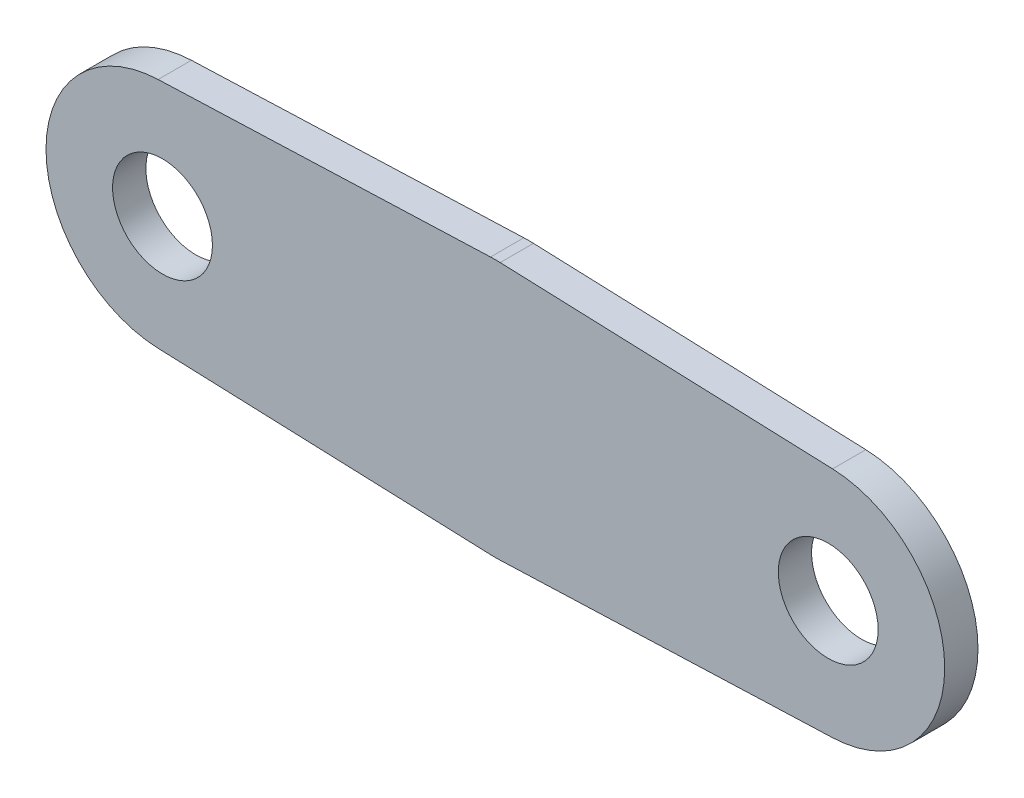
SolidWorks part; units mm, degrees
ref_plane "Płaszczyzna XY" through (0, 0, 0) normal (0, 0, 1) x (1, 0, 0)
ref_plane "Płaszczyzna XZ" through (0, 0, 0) normal (0, 1, 0) x (1, 0, 0)
ref_plane "Płaszczyzna YZ" through (0, 0, 0) normal (1, 0, 0) x (0, 0, -1)
sketch "Szkic1" plane through (0, 0, 0) normal (0, 0, 1) x (1, 0, 0)
  line L0 (-0.2906, 7.7445) -> (-20.2625, 6.9951)
  line L1 (-0.2906, -7.7445) -> (-20.2625, -6.9951)
  line L2 (0.2906, 7.7445) -> (20.2625, 6.9951)
  line L3 (0, 0) -> (0, -3.6778) construction
  line L10 (0.2906, -7.7445) -> (20.2625, -6.9951)
  arc A0 (-0.2906, -7.7445) -> (0.2906, -7.7445) centre (0, 0) ccw
  arc A2 (-20.2625, 6.9951) -> (-20.2625, -6.9951) centre (-20, 0) ccw
  arc A3 (20.2625, -6.9951) -> (20.2625, 6.9951) centre (20, 0) ccw
  arc A4 (0.2906, 7.7445) -> (-0.2906, 7.7445) centre (0, 0) ccw
  circle A5 centre (-20, 0) radius 3
  circle A10 centre (20, 0) radius 3
  dimension "D2" = 15.5
  dimension "D3" = 14
  dimension "D4" = 6
  dimension "D1" = 40
extrude "Dodanie-wyciągnięcie1" add sketch "Szkic1" along normal blind 2
sketch "Szkic2" [suppressed] plane through (0, 0, 1) normal (0, 0, 1) x (1, 0, 0)
  line L0 (-20, 3) -> (-26.3246, 3)
  line L1 (-20, -3) -> (-26.3246, -3)
  circle A0 centre (-20, 0) radius 3 construction
  arc A1 (-20.2625, 6.9951) -> (-20.2625, -6.9951) centre (-20, 0) ccw construction
  arc A2 (-26.3246, -3) -> (-26.3246, 3) centre (-20, 0) cw
  arc A3 (-20, -3) -> (-20, 3) centre (-20, 0) cw
extrude "Wytnij-wyciągnięcie1" [suppressed] cut sketch "Szkic2" against normal through all
sketch "Szkic3" [suppressed] plane through (0, 0, 1) normal (0, 0, 1) x (1, 0, 0)
  line L0 (0.2906, -7.7445) -> (20.2625, -6.9951) construction
  line L1 (16.3038, -7.1436) -> (20.2625, -6.9951)
  arc A0 (17, 0) -> (16.3038, -7.1436) centre (-20, 0) cw
  circle A1 centre (20, 0) radius 3 construction
  arc A2 (23, 0) -> (22.5, -6.5383) centre (-20, 0) cw
  arc A3 (20.2625, -6.9951) -> (20.2625, 6.9951) centre (20, 0) ccw construction
  arc A4 (17, 0) -> (23, 0) centre (20, 0) ccw
  arc A5 (20.2625, -6.9951) -> (22.5, -6.5383) centre (20, 0) ccw
  line M5 (0.2906, -7.7445) -> (20.2625, -6.9951)
  arc M6 (20.2625, -6.9951) -> (20.2625, 6.9951) centre (20, 0) ccw
  circle M13 centre (20, 0) radius 3
extrude "Wytnij-wyciągnięcie3" [suppressed] cut sketch "Szkic3" against normal through all contours A2 A0 M13 M5 M6
